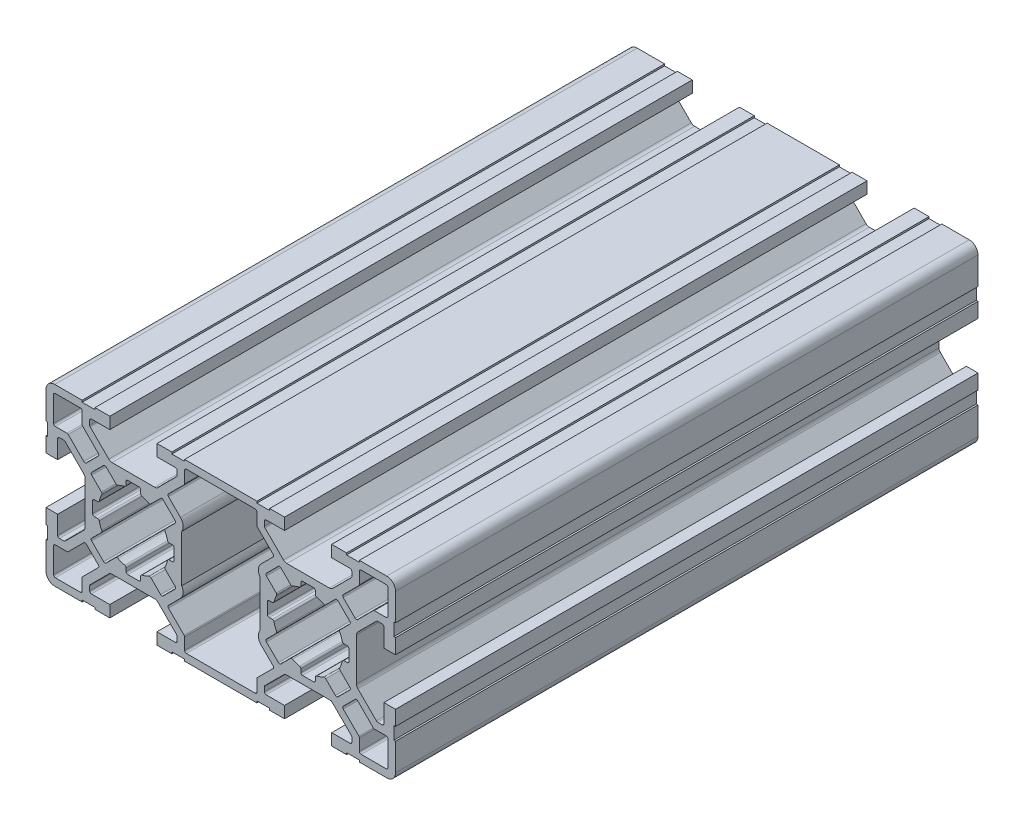
SolidWorks part; units mm, degrees
ref_plane "Plano frontal" through (0, 0, 0) normal (0, 0, 1) x (1, 0, 0)
ref_plane "Plano superior" through (0, 0, 0) normal (0, 1, 0) x (1, 0, 0)
ref_plane "Plano direito" through (0, 0, 0) normal (1, 0, 0) x (0, 0, -1)
sketch "Esboço1" plane through (0, 0, 0) normal (1, 0, 0) x (0, 0, -1)
  line L0 (-50, 0) -> (50, 0)
  point P4 (0, 0)
  dimension "D1" = 100
other "Retangular PF30-02 - PERFIL 3060 BÁSICO(1)"
ref_plane "Plano1" through (0, 0, 50) normal (0, 0, -1) x (0, -1, 0)
sketch "Sketch1" plane through (0, 0, 50) normal (0, 0, -1) x (0, -1, 0)
  line L0 (-4.05, 30) -> (-4.05, 28)
  line L1 (-6.0258, -23.5007) -> (-8.7121, -26.187)
  line L2 (-8.8, -26.3991) -> (-8.8, -28.4)
  line L3 (-9.1, -28.7) -> (-13.4, -28.7)
  line L4 (-13.7, -28.4) -> (-13.7, -24.1)
  line L5 (-13.4, -23.8) -> (-11.3991, -23.8)
  line L6 (-11.187, -23.7121) -> (-8.5007, -21.0258)
  line L7 (-8.0765, -21.0258) -> (-6.0258, -23.0765)
  line L8 (13.7, 5.9) -> (13.7, -5.9)
  line L9 (13.4, -6.2) -> (11.3991, -6.2)
  line L10 (11.187, -6.2879) -> (8.5007, -8.9742)
  line L11 (8.0765, -8.9742) -> (6.0258, -6.9235)
  line L12 (4.0435, -6.7) -> (-4.0435, -6.7)
  line L13 (-6.0258, -6.9235) -> (-8.0765, -8.9742)
  line L14 (-8.5007, -8.9742) -> (-11.187, -6.2879)
  line L15 (-11.3991, -6.2) -> (-13.4, -6.2)
  line L16 (-13.7, -5.9) -> (-13.7, 5.9)
  line L17 (-13.4, 6.2) -> (-11.3991, 6.2)
  line L18 (-11.187, 6.2879) -> (-8.5007, 8.9742)
  line L19 (-8.0765, 8.9742) -> (-6.0258, 6.9235)
  line L20 (-4.0435, 6.7) -> (4.0435, 6.7)
  line L21 (6.0258, 6.9235) -> (8.0765, 8.9742)
  line L22 (8.5007, 8.9742) -> (11.187, 6.2879)
  line L23 (11.3991, 6.2) -> (13.4, 6.2)
  line L24 (8.0765, 21.0258) -> (6.0258, 23.0765)
  line L25 (6.0258, 23.5007) -> (8.7121, 26.187)
  line L26 (8.8, 26.3991) -> (8.8, 28.4)
  line L27 (9.1, 28.7) -> (13.4, 28.7)
  line L28 (13.7, 28.4) -> (13.7, 24.1)
  line L29 (13.4, 23.8) -> (11.3991, 23.8)
  line L30 (11.187, 23.7121) -> (8.5007, 21.0258)
  line L31 (-8.7121, 26.187) -> (-6.0258, 23.5007)
  line L32 (-6.0258, 23.0765) -> (-8.0765, 21.0258)
  line L33 (-8.5007, 21.0258) -> (-11.187, 23.7121)
  line L34 (-11.3991, 23.8) -> (-13.4, 23.8)
  line L35 (-13.7, 24.1) -> (-13.7, 28.4)
  line L36 (-13.4, 28.7) -> (-9.1, 28.7)
  line L37 (-8.8, 28.4) -> (-8.8, 26.3991)
  line L38 (-3.0123, 9.5129) -> (-4.6823, 7.8428)
  line L39 (-5.1066, 7.8428) -> (-7.1572, 9.8934)
  line L40 (-7.1572, 10.3177) -> (-5.4871, 11.9877)
  line L41 (-6.1579, 13.75) -> (-6.7, 13.75)
  line L42 (-7, 14.05) -> (-7, 15.95)
  line L43 (-6.7, 16.25) -> (-6.1579, 16.25)
  line L44 (-5.4871, 18.0123) -> (-7.1572, 19.6823)
  line L45 (-7.1572, 20.1066) -> (-5.1066, 22.1572)
  line L46 (-4.6823, 22.1572) -> (-3.0123, 20.4871)
  line L47 (-1.25, 21.1579) -> (-1.25, 21.7)
  line L48 (-0.95, 22) -> (0.95, 22)
  line L49 (1.25, 21.7) -> (1.25, 21.1579)
  line L50 (3.0123, 20.4871) -> (4.6823, 22.1572)
  line L51 (5.1066, 22.1572) -> (7.1572, 20.1066)
  line L52 (7.1572, 19.6823) -> (5.4871, 18.0123)
  line L53 (6.1579, 16.25) -> (6.7, 16.25)
  line L54 (7, 15.95) -> (7, 14.05)
  line L55 (6.7, 13.75) -> (6.1579, 13.75)
  line L56 (5.4871, 11.9877) -> (7.1572, 10.3177)
  line L57 (7.1572, 9.8934) -> (5.1066, 7.8428)
  line L58 (4.6823, 7.8428) -> (3.0123, 9.5129)
  line L59 (1.25, 8.8421) -> (1.25, 8.3)
  line L60 (0.95, 8) -> (-0.95, 8)
  line L61 (-1.25, 8.3) -> (-1.25, 8.8421)
  line L62 (-1.25, -8.8421) -> (-1.25, -8.3)
  line L63 (-0.95, -8) -> (0.95, -8)
  line L64 (1.25, -8.3) -> (1.25, -8.8421)
  line L65 (3.0123, -9.5129) -> (4.6823, -7.8428)
  line L66 (5.1066, -7.8428) -> (7.1572, -9.8934)
  line L67 (7.1572, -10.3177) -> (5.4871, -11.9877)
  line L68 (6.1579, -13.75) -> (6.7, -13.75)
  line L69 (7, -14.05) -> (7, -15.95)
  line L70 (6.7, -16.25) -> (6.1579, -16.25)
  line L71 (5.4871, -18.0123) -> (7.1572, -19.6823)
  line L72 (7.1572, -20.1066) -> (5.1066, -22.1572)
  line L73 (4.6823, -22.1572) -> (3.0123, -20.4871)
  line L74 (1.25, -21.1579) -> (1.25, -21.7)
  line L75 (0.95, -22) -> (-0.95, -22)
  line L76 (-1.25, -21.7) -> (-1.25, -21.1579)
  line L77 (-3.0123, -20.4871) -> (-4.6823, -22.1572)
  line L78 (-5.1066, -22.1572) -> (-7.1572, -20.1066)
  line L79 (-7.1572, -19.6823) -> (-5.4871, -18.0123)
  line L80 (-6.1579, -16.25) -> (-6.7, -16.25)
  line L81 (-7, -15.95) -> (-7, -14.05)
  line L82 (-6.7, -13.75) -> (-6.1579, -13.75)
  line L83 (-5.4871, -11.9877) -> (-7.1572, -10.3177)
  line L84 (-7.1572, -9.8934) -> (-5.1066, -7.8428)
  line L85 (-4.6823, -7.8428) -> (-3.0123, -9.5129)
  line L86 (6.0258, -23.0765) -> (8.0765, -21.0258)
  line L87 (8.5007, -21.0258) -> (11.187, -23.7121)
  line L88 (11.3991, -23.8) -> (13.4, -23.8)
  line L89 (13.7, -24.1) -> (13.7, -28.4)
  line L90 (13.4, -28.7) -> (9.1, -28.7)
  line L91 (8.8, -28.4) -> (8.8, -26.3991)
  line L92 (8.7121, -26.187) -> (6.0258, -23.5007)
  line L93 (15, -6.2) -> (15, 6.2)
  line L94 (15, 6.2) -> (14.7, 6.2)
  line L95 (14.7, 6.2) -> (14.7, 8.4)
  line L96 (14.7, 8.4) -> (15, 8.4)
  line L97 (15, 8.4) -> (15, 10.95)
  line L98 (15, 10.95) -> (13, 10.95)
  line L99 (13, 10.95) -> (13, 7.8)
  line L100 (12.7, 7.5) -> (11.9376, 7.5)
  line L101 (11.7255, 7.5879) -> (8.5343, 10.779)
  line L102 (8.3, 11.3447) -> (8.3, 18.6553)
  line L103 (8.5343, 19.221) -> (11.7255, 22.4121)
  line L104 (11.9376, 22.5) -> (12.7, 22.5)
  line L105 (13, 22.2) -> (13, 19.05)
  line L106 (13, 19.05) -> (15, 19.05)
  line L107 (15, 19.05) -> (15, 21.6)
  line L108 (15, 21.6) -> (14.7, 21.6)
  line L109 (14.7, 21.6) -> (14.7, 23.8)
  line L110 (14.7, 23.8) -> (15, 23.8)
  line L111 (15, 23.8) -> (15, 28.5)
  line L112 (13.5, 30) -> (8.8, 30)
  line L113 (8.8, 30) -> (8.8, 29.7)
  line L114 (8.8, 29.7) -> (6.6, 29.7)
  line L115 (6.6, 29.7) -> (6.6, 30)
  line L116 (6.6, 30) -> (4.05, 30)
  line L117 (4.05, 30) -> (4.05, 28)
  line L118 (4.05, 28) -> (7.2, 28)
  line L119 (7.5, 27.7) -> (7.5, 26.9376)
  line L120 (7.4121, 26.7255) -> (4.221, 23.5343)
  line L121 (3.6553, 23.3) -> (-3.6553, 23.3)
  line L122 (-4.221, 23.5343) -> (-7.4121, 26.7255)
  line L123 (-7.5, 26.9376) -> (-7.5, 27.7)
  line L124 (-7.2, 28) -> (-4.05, 28)
  line L125 (-4.05, 30) -> (-6.6, 30)
  line L126 (-6.6, 30) -> (-6.6, 29.7)
  line L127 (-6.6, 29.7) -> (-8.8, 29.7)
  line L128 (-8.8, 29.7) -> (-8.8, 30)
  line L129 (-8.8, 30) -> (-13.5, 30)
  line L130 (-15, 28.5) -> (-15, 23.8)
  line L131 (-15, 23.8) -> (-14.7, 23.8)
  line L132 (-14.7, 23.8) -> (-14.7, 21.6)
  line L133 (-14.7, 21.6) -> (-15, 21.6)
  line L134 (-15, 21.6) -> (-15, 19.05)
  line L135 (-15, 19.05) -> (-13, 19.05)
  line L136 (-13, 19.05) -> (-13, 22.2)
  line L137 (-12.7, 22.5) -> (-11.9376, 22.5)
  line L138 (-11.7255, 22.4121) -> (-8.5343, 19.221)
  line L139 (-8.3, 18.6553) -> (-8.3, 11.3447)
  line L140 (-8.5343, 10.779) -> (-11.7255, 7.5879)
  line L141 (-11.9376, 7.5) -> (-12.7, 7.5)
  line L142 (-13, 7.8) -> (-13, 10.95)
  line L143 (-13, 10.95) -> (-15, 10.95)
  line L144 (-15, 10.95) -> (-15, 8.4)
  line L145 (-15, 8.4) -> (-14.7, 8.4)
  line L146 (-14.7, 8.4) -> (-14.7, 6.2)
  line L147 (-14.7, 6.2) -> (-15, 6.2)
  line L148 (-15, 6.2) -> (-15, -6.2)
  line L149 (-15, -6.2) -> (-14.7, -6.2)
  line L150 (-14.7, -6.2) -> (-14.7, -8.4)
  line L151 (-14.7, -8.4) -> (-15, -8.4)
  line L152 (-15, -8.4) -> (-15, -10.95)
  line L153 (-15, -10.95) -> (-13, -10.95)
  line L154 (-13, -10.95) -> (-13, -7.8)
  line L155 (-12.7, -7.5) -> (-11.9376, -7.5)
  line L156 (-11.7255, -7.5879) -> (-8.5343, -10.779)
  line L157 (-8.3, -11.3447) -> (-8.3, -18.6553)
  line L158 (-8.5343, -19.221) -> (-11.7255, -22.4121)
  line L159 (-11.9376, -22.5) -> (-12.7, -22.5)
  line L160 (-13, -22.2) -> (-13, -19.05)
  line L161 (-13, -19.05) -> (-15, -19.05)
  line L162 (-15, -19.05) -> (-15, -21.6)
  line L163 (-15, -21.6) -> (-14.7, -21.6)
  line L164 (-14.7, -21.6) -> (-14.7, -23.8)
  line L165 (-14.7, -23.8) -> (-15, -23.8)
  line L166 (-15, -23.8) -> (-15, -28.5)
  line L167 (-13.5, -30) -> (-8.8, -30)
  line L168 (-8.8, -30) -> (-8.8, -29.7)
  line L169 (-8.8, -29.7) -> (-6.6, -29.7)
  line L170 (-6.6, -29.7) -> (-6.6, -30)
  line L171 (-6.6, -30) -> (-4.05, -30)
  line L172 (-4.05, -30) -> (-4.05, -28)
  line L173 (-4.05, -28) -> (-7.2, -28)
  line L174 (-7.5, -27.7) -> (-7.5, -26.9376)
  line L175 (-7.4121, -26.7255) -> (-4.221, -23.5343)
  line L176 (-3.6553, -23.3) -> (3.6553, -23.3)
  line L177 (4.221, -23.5343) -> (7.4121, -26.7255)
  line L178 (7.5, -26.9376) -> (7.5, -27.7)
  line L179 (7.2, -28) -> (4.05, -28)
  line L180 (4.05, -28) -> (4.05, -30)
  line L181 (4.05, -30) -> (6.6, -30)
  line L182 (6.6, -30) -> (6.6, -29.7)
  line L183 (6.6, -29.7) -> (8.8, -29.7)
  line L184 (8.8, -29.7) -> (8.8, -30)
  line L185 (8.8, -30) -> (13.5, -30)
  line L186 (15, -28.5) -> (15, -23.8)
  line L187 (15, -23.8) -> (14.7, -23.8)
  line L188 (14.7, -23.8) -> (14.7, -21.6)
  line L189 (14.7, -21.6) -> (15, -21.6)
  line L190 (15, -21.6) -> (15, -19.05)
  line L191 (15, -19.05) -> (13, -19.05)
  line L192 (13, -19.05) -> (13, -22.2)
  line L193 (12.7, -22.5) -> (11.9376, -22.5)
  line L194 (11.7255, -22.4121) -> (8.5343, -19.221)
  line L195 (8.3, -18.6553) -> (8.3, -11.3447)
  line L196 (8.5343, -10.779) -> (11.7255, -7.5879)
  line L197 (11.9376, -7.5) -> (12.7, -7.5)
  line L198 (13, -7.8) -> (13, -10.95)
  line L199 (13, -10.95) -> (15, -10.95)
  line L200 (15, -10.95) -> (15, -8.4)
  line L201 (15, -8.4) -> (14.7, -8.4)
  line L202 (14.7, -8.4) -> (14.7, -6.2)
  line L203 (14.7, -6.2) -> (15, -6.2)
  arc A0 (-8.7121, -26.187) -> (-8.8, -26.3991) centre (-8.5, -26.3991) ccw
  arc A1 (-9.1, -28.7) -> (-8.8, -28.4) centre (-9.1, -28.4) ccw
  arc A2 (-13.7, -28.4) -> (-13.4, -28.7) centre (-13.4, -28.4) ccw
  arc A3 (-13.4, -23.8) -> (-13.7, -24.1) centre (-13.4, -24.1) ccw
  arc A4 (-11.3991, -23.8) -> (-11.187, -23.7121) centre (-11.3991, -23.5) ccw
  arc A5 (-8.0765, -21.0258) -> (-8.5007, -21.0258) centre (-8.2886, -21.238) ccw
  arc A6 (-6.0258, -23.5007) -> (-6.0258, -23.0765) centre (-6.238, -23.2886) ccw
  arc A7 (13.4, -6.2) -> (13.7, -5.9) centre (13.4, -5.9) ccw
  arc A8 (11.3991, -6.2) -> (11.187, -6.2879) centre (11.3991, -6.5) ccw
  arc A9 (8.0765, -8.9742) -> (8.5007, -8.9742) centre (8.2886, -8.762) ccw
  arc A10 (6.0258, -6.9235) -> (4.0435, -6.7) centre (4.8945, -8.0549) ccw
  arc A11 (-4.0435, -6.7) -> (-6.0258, -6.9235) centre (-4.8945, -8.0549) ccw
  arc A12 (-8.5007, -8.9742) -> (-8.0765, -8.9742) centre (-8.2886, -8.762) ccw
  arc A13 (-11.187, -6.2879) -> (-11.3991, -6.2) centre (-11.3991, -6.5) ccw
  arc A14 (-13.7, -5.9) -> (-13.4, -6.2) centre (-13.4, -5.9) ccw
  arc A15 (-13.4, 6.2) -> (-13.7, 5.9) centre (-13.4, 5.9) ccw
  arc A16 (-11.3991, 6.2) -> (-11.187, 6.2879) centre (-11.3991, 6.5) ccw
  arc A17 (-8.0765, 8.9742) -> (-8.5007, 8.9742) centre (-8.2886, 8.762) ccw
  arc A18 (-6.0258, 6.9235) -> (-4.0435, 6.7) centre (-4.8945, 8.0549) ccw
  arc A19 (4.0435, 6.7) -> (6.0258, 6.9235) centre (4.8945, 8.0549) ccw
  arc A20 (8.5007, 8.9742) -> (8.0765, 8.9742) centre (8.2886, 8.762) ccw
  arc A21 (11.187, 6.2879) -> (11.3991, 6.2) centre (11.3991, 6.5) ccw
  arc A22 (13.7, 5.9) -> (13.4, 6.2) centre (13.4, 5.9) ccw
  arc A23 (6.0258, 23.5007) -> (6.0258, 23.0765) centre (6.238, 23.2886) ccw
  arc A24 (8.7121, 26.187) -> (8.8, 26.3991) centre (8.5, 26.3991) ccw
  arc A25 (9.1, 28.7) -> (8.8, 28.4) centre (9.1, 28.4) ccw
  arc A26 (13.7, 28.4) -> (13.4, 28.7) centre (13.4, 28.4) ccw
  arc A27 (13.4, 23.8) -> (13.7, 24.1) centre (13.4, 24.1) ccw
  arc A28 (11.3991, 23.8) -> (11.187, 23.7121) centre (11.3991, 23.5) ccw
  arc A29 (8.0765, 21.0258) -> (8.5007, 21.0258) centre (8.2886, 21.238) ccw
  arc A30 (-6.0258, 23.0765) -> (-6.0258, 23.5007) centre (-6.238, 23.2886) ccw
  arc A31 (-8.5007, 21.0258) -> (-8.0765, 21.0258) centre (-8.2886, 21.238) ccw
  arc A32 (-11.187, 23.7121) -> (-11.3991, 23.8) centre (-11.3991, 23.5) ccw
  arc A33 (-13.7, 24.1) -> (-13.4, 23.8) centre (-13.4, 24.1) ccw
  arc A34 (-13.4, 28.7) -> (-13.7, 28.4) centre (-13.4, 28.4) ccw
  arc A35 (-8.8, 28.4) -> (-9.1, 28.7) centre (-9.1, 28.4) ccw
  arc A36 (-8.8, 26.3991) -> (-8.7121, 26.187) centre (-8.5, 26.3991) ccw
  arc A37 (-2.6678, 9.57) -> (-3.0123, 9.5129) centre (-2.8001, 9.3007) ccw
  arc A38 (-5.1066, 7.8428) -> (-4.6823, 7.8428) centre (-4.8945, 8.0549) ccw
  arc A39 (-7.1572, 10.3177) -> (-7.1572, 9.8934) centre (-6.9451, 10.1055) ccw
  arc A40 (-5.4871, 11.9877) -> (-5.43, 12.3322) centre (-5.6993, 12.1999) ccw
  arc A41 (-5.867, 13.5232) -> (-5.43, 12.3322) centre (0, 15) ccw
  arc A42 (-5.867, 13.5232) -> (-6.1579, 13.75) centre (-6.1579, 13.45) ccw
  arc A43 (-7, 14.05) -> (-6.7, 13.75) centre (-6.7, 14.05) ccw
  arc A44 (-6.7, 16.25) -> (-7, 15.95) centre (-6.7, 15.95) ccw
  arc A45 (-6.1579, 16.25) -> (-5.867, 16.4768) centre (-6.1579, 16.55) ccw
  arc A46 (-5.43, 17.6678) -> (-5.867, 16.4768) centre (0, 15) ccw
  arc A47 (-5.43, 17.6678) -> (-5.4871, 18.0123) centre (-5.6993, 17.8001) ccw
  arc A48 (-7.1572, 20.1066) -> (-7.1572, 19.6823) centre (-6.9451, 19.8945) ccw
  arc A49 (-4.6823, 22.1572) -> (-5.1066, 22.1572) centre (-4.8945, 21.9451) ccw
  arc A50 (-3.0123, 20.4871) -> (-2.6678, 20.43) centre (-2.8001, 20.6993) ccw
  arc A51 (-1.4768, 20.867) -> (-2.6678, 20.43) centre (0, 15) ccw
  arc A52 (-1.4768, 20.867) -> (-1.25, 21.1579) centre (-1.55, 21.1579) ccw
  arc A53 (-0.95, 22) -> (-1.25, 21.7) centre (-0.95, 21.7) ccw
  arc A54 (1.25, 21.7) -> (0.95, 22) centre (0.95, 21.7) ccw
  arc A55 (1.25, 21.1579) -> (1.4768, 20.867) centre (1.55, 21.1579) ccw
  arc A56 (2.6678, 20.43) -> (1.4768, 20.867) centre (0, 15) ccw
  arc A57 (2.6678, 20.43) -> (3.0123, 20.4871) centre (2.8001, 20.6993) ccw
  arc A58 (5.1066, 22.1572) -> (4.6823, 22.1572) centre (4.8945, 21.9451) ccw
  arc A59 (7.1572, 19.6823) -> (7.1572, 20.1066) centre (6.9451, 19.8945) ccw
  arc A60 (5.4871, 18.0123) -> (5.43, 17.6678) centre (5.6993, 17.8001) ccw
  arc A61 (5.867, 16.4768) -> (5.43, 17.6678) centre (0, 15) ccw
  arc A62 (5.867, 16.4768) -> (6.1579, 16.25) centre (6.1579, 16.55) ccw
  arc A63 (7, 15.95) -> (6.7, 16.25) centre (6.7, 15.95) ccw
  arc A64 (6.7, 13.75) -> (7, 14.05) centre (6.7, 14.05) ccw
  arc A65 (6.1579, 13.75) -> (5.867, 13.5232) centre (6.1579, 13.45) ccw
  arc A66 (5.43, 12.3322) -> (5.867, 13.5232) centre (0, 15) ccw
  arc A67 (5.43, 12.3322) -> (5.4871, 11.9877) centre (5.6993, 12.1999) ccw
  arc A68 (7.1572, 9.8934) -> (7.1572, 10.3177) centre (6.9451, 10.1055) ccw
  arc A69 (4.6823, 7.8428) -> (5.1066, 7.8428) centre (4.8945, 8.0549) ccw
  arc A70 (3.0123, 9.5129) -> (2.6678, 9.57) centre (2.8001, 9.3007) ccw
  arc A71 (1.4768, 9.133) -> (2.6678, 9.57) centre (0, 15) ccw
  arc A72 (1.4768, 9.133) -> (1.25, 8.8421) centre (1.55, 8.8421) ccw
  arc A73 (0.95, 8) -> (1.25, 8.3) centre (0.95, 8.3) ccw
  arc A74 (-1.25, 8.3) -> (-0.95, 8) centre (-0.95, 8.3) ccw
  arc A75 (-1.25, 8.8421) -> (-1.4768, 9.133) centre (-1.55, 8.8421) ccw
  arc A76 (-2.6678, 9.57) -> (-1.4768, 9.133) centre (0, 15) ccw
  arc A77 (-3.0123, -9.5129) -> (-2.6678, -9.57) centre (-2.8001, -9.3007) ccw
  arc A78 (-1.4768, -9.133) -> (-2.6678, -9.57) centre (0, -15) ccw
  arc A79 (-1.4768, -9.133) -> (-1.25, -8.8421) centre (-1.55, -8.8421) ccw
  arc A80 (-0.95, -8) -> (-1.25, -8.3) centre (-0.95, -8.3) ccw
  arc A81 (1.25, -8.3) -> (0.95, -8) centre (0.95, -8.3) ccw
  arc A82 (1.25, -8.8421) -> (1.4768, -9.133) centre (1.55, -8.8421) ccw
  arc A83 (2.6678, -9.57) -> (1.4768, -9.133) centre (0, -15) ccw
  arc A84 (2.6678, -9.57) -> (3.0123, -9.5129) centre (2.8001, -9.3007) ccw
  arc A85 (5.1066, -7.8428) -> (4.6823, -7.8428) centre (4.8945, -8.0549) ccw
  arc A86 (7.1572, -10.3177) -> (7.1572, -9.8934) centre (6.9451, -10.1055) ccw
  arc A87 (5.4871, -11.9877) -> (5.43, -12.3322) centre (5.6993, -12.1999) ccw
  arc A88 (5.867, -13.5232) -> (5.43, -12.3322) centre (0, -15) ccw
  arc A89 (5.867, -13.5232) -> (6.1579, -13.75) centre (6.1579, -13.45) ccw
  arc A90 (7, -14.05) -> (6.7, -13.75) centre (6.7, -14.05) ccw
  arc A91 (6.7, -16.25) -> (7, -15.95) centre (6.7, -15.95) ccw
  arc A92 (6.1579, -16.25) -> (5.867, -16.4768) centre (6.1579, -16.55) ccw
  arc A93 (5.43, -17.6678) -> (5.867, -16.4768) centre (0, -15) ccw
  arc A94 (5.43, -17.6678) -> (5.4871, -18.0123) centre (5.6993, -17.8001) ccw
  arc A95 (7.1572, -20.1066) -> (7.1572, -19.6823) centre (6.9451, -19.8945) ccw
  arc A96 (4.6823, -22.1572) -> (5.1066, -22.1572) centre (4.8945, -21.9451) ccw
  arc A97 (3.0123, -20.4871) -> (2.6678, -20.43) centre (2.8001, -20.6993) ccw
  arc A98 (1.4768, -20.867) -> (2.6678, -20.43) centre (0, -15) ccw
  arc A99 (1.4768, -20.867) -> (1.25, -21.1579) centre (1.55, -21.1579) ccw
  arc A100 (0.95, -22) -> (1.25, -21.7) centre (0.95, -21.7) ccw
  arc A101 (-1.25, -21.7) -> (-0.95, -22) centre (-0.95, -21.7) ccw
  arc A102 (-1.25, -21.1579) -> (-1.4768, -20.867) centre (-1.55, -21.1579) ccw
  arc A103 (-2.6678, -20.43) -> (-1.4768, -20.867) centre (0, -15) ccw
  arc A104 (-2.6678, -20.43) -> (-3.0123, -20.4871) centre (-2.8001, -20.6993) ccw
  arc A105 (-5.1066, -22.1572) -> (-4.6823, -22.1572) centre (-4.8945, -21.9451) ccw
  arc A106 (-7.1572, -19.6823) -> (-7.1572, -20.1066) centre (-6.9451, -19.8945) ccw
  arc A107 (-5.4871, -18.0123) -> (-5.43, -17.6678) centre (-5.6993, -17.8001) ccw
  arc A108 (-5.867, -16.4768) -> (-5.43, -17.6678) centre (0, -15) ccw
  arc A109 (-5.867, -16.4768) -> (-6.1579, -16.25) centre (-6.1579, -16.55) ccw
  arc A110 (-7, -15.95) -> (-6.7, -16.25) centre (-6.7, -15.95) ccw
  arc A111 (-6.7, -13.75) -> (-7, -14.05) centre (-6.7, -14.05) ccw
  arc A112 (-6.1579, -13.75) -> (-5.867, -13.5232) centre (-6.1579, -13.45) ccw
  arc A113 (-5.43, -12.3322) -> (-5.867, -13.5232) centre (0, -15) ccw
  arc A114 (-5.43, -12.3322) -> (-5.4871, -11.9877) centre (-5.6993, -12.1999) ccw
  arc A115 (-7.1572, -9.8934) -> (-7.1572, -10.3177) centre (-6.9451, -10.1055) ccw
  arc A116 (-4.6823, -7.8428) -> (-5.1066, -7.8428) centre (-4.8945, -8.0549) ccw
  arc A117 (8.5007, -21.0258) -> (8.0765, -21.0258) centre (8.2886, -21.238) ccw
  arc A118 (11.187, -23.7121) -> (11.3991, -23.8) centre (11.3991, -23.5) ccw
  arc A119 (13.7, -24.1) -> (13.4, -23.8) centre (13.4, -24.1) ccw
  arc A120 (13.4, -28.7) -> (13.7, -28.4) centre (13.4, -28.4) ccw
  arc A121 (8.8, -28.4) -> (9.1, -28.7) centre (9.1, -28.4) ccw
  arc A122 (8.8, -26.3991) -> (8.7121, -26.187) centre (8.5, -26.3991) ccw
  arc A123 (6.0258, -23.0765) -> (6.0258, -23.5007) centre (6.238, -23.2886) ccw
  arc A124 (12.7, 7.5) -> (13, 7.8) centre (12.7, 7.8) ccw
  arc A125 (11.7255, 7.5879) -> (11.9376, 7.5) centre (11.9376, 7.8) ccw
  arc A126 (8.3, 11.3447) -> (8.5343, 10.779) centre (9.1, 11.3447) ccw
  arc A127 (8.5343, 19.221) -> (8.3, 18.6553) centre (9.1, 18.6553) ccw
  arc A128 (11.9376, 22.5) -> (11.7255, 22.4121) centre (11.9376, 22.2) ccw
  arc A129 (13, 22.2) -> (12.7, 22.5) centre (12.7, 22.2) ccw
  arc A130 (15, 28.5) -> (13.5, 30) centre (13.5, 28.5) ccw
  arc A131 (7.5, 27.7) -> (7.2, 28) centre (7.2, 27.7) ccw
  arc A132 (7.4121, 26.7255) -> (7.5, 26.9376) centre (7.2, 26.9376) ccw
  arc A133 (3.6553, 23.3) -> (4.221, 23.5343) centre (3.6553, 24.1) ccw
  arc A134 (-4.221, 23.5343) -> (-3.6553, 23.3) centre (-3.6553, 24.1) ccw
  arc A135 (-7.5, 26.9376) -> (-7.4121, 26.7255) centre (-7.2, 26.9376) ccw
  arc A136 (-7.2, 28) -> (-7.5, 27.7) centre (-7.2, 27.7) ccw
  arc A137 (-13.5, 30) -> (-15, 28.5) centre (-13.5, 28.5) ccw
  arc A138 (-12.7, 22.5) -> (-13, 22.2) centre (-12.7, 22.2) ccw
  arc A139 (-11.7255, 22.4121) -> (-11.9376, 22.5) centre (-11.9376, 22.2) ccw
  arc A140 (-8.3, 18.6553) -> (-8.5343, 19.221) centre (-9.1, 18.6553) ccw
  arc A141 (-8.5343, 10.779) -> (-8.3, 11.3447) centre (-9.1, 11.3447) ccw
  arc A142 (-11.9376, 7.5) -> (-11.7255, 7.5879) centre (-11.9376, 7.8) ccw
  arc A143 (-13, 7.8) -> (-12.7, 7.5) centre (-12.7, 7.8) ccw
  arc A144 (-12.7, -7.5) -> (-13, -7.8) centre (-12.7, -7.8) ccw
  arc A145 (-11.7255, -7.5879) -> (-11.9376, -7.5) centre (-11.9376, -7.8) ccw
  arc A146 (-8.3, -11.3447) -> (-8.5343, -10.779) centre (-9.1, -11.3447) ccw
  arc A147 (-8.5343, -19.221) -> (-8.3, -18.6553) centre (-9.1, -18.6553) ccw
  arc A148 (-11.9376, -22.5) -> (-11.7255, -22.4121) centre (-11.9376, -22.2) ccw
  arc A149 (-13, -22.2) -> (-12.7, -22.5) centre (-12.7, -22.2) ccw
  arc A150 (-15, -28.5) -> (-13.5, -30) centre (-13.5, -28.5) ccw
  arc A151 (-7.5, -27.7) -> (-7.2, -28) centre (-7.2, -27.7) ccw
  arc A152 (-7.4121, -26.7255) -> (-7.5, -26.9376) centre (-7.2, -26.9376) ccw
  arc A153 (-3.6553, -23.3) -> (-4.221, -23.5343) centre (-3.6553, -24.1) ccw
  arc A154 (4.221, -23.5343) -> (3.6553, -23.3) centre (3.6553, -24.1) ccw
  arc A155 (7.5, -26.9376) -> (7.4121, -26.7255) centre (7.2, -26.9376) ccw
  arc A156 (7.2, -28) -> (7.5, -27.7) centre (7.2, -27.7) ccw
  arc A157 (13.5, -30) -> (15, -28.5) centre (13.5, -28.5) ccw
  arc A158 (12.7, -22.5) -> (13, -22.2) centre (12.7, -22.2) ccw
  arc A159 (11.7255, -22.4121) -> (11.9376, -22.5) centre (11.9376, -22.2) ccw
  arc A160 (8.3, -18.6553) -> (8.5343, -19.221) centre (9.1, -18.6553) ccw
  arc A161 (8.5343, -10.779) -> (8.3, -11.3447) centre (9.1, -11.3447) ccw
  arc A162 (11.9376, -7.5) -> (11.7255, -7.5879) centre (11.9376, -7.8) ccw
  arc A163 (13, -7.8) -> (12.7, -7.5) centre (12.7, -7.8) ccw
  point P0 (-15, 30)
  point P1 (0, 30)
  point P2 (15, 30)
  point P3 (15, 15)
  point P4 (15, 0)
  point P5 (15, -15)
  point P6 (15, -30)
  point P7 (0, -30)
  point P8 (-15, -30)
  point P9 (-15, -15)
  point P10 (-15, 0)
  point P11 (-15, 15)
  point P12 (0, 0)
  point P13 (0, 15)
  point P14 (0, -15)
  point P529 (0, 0)
